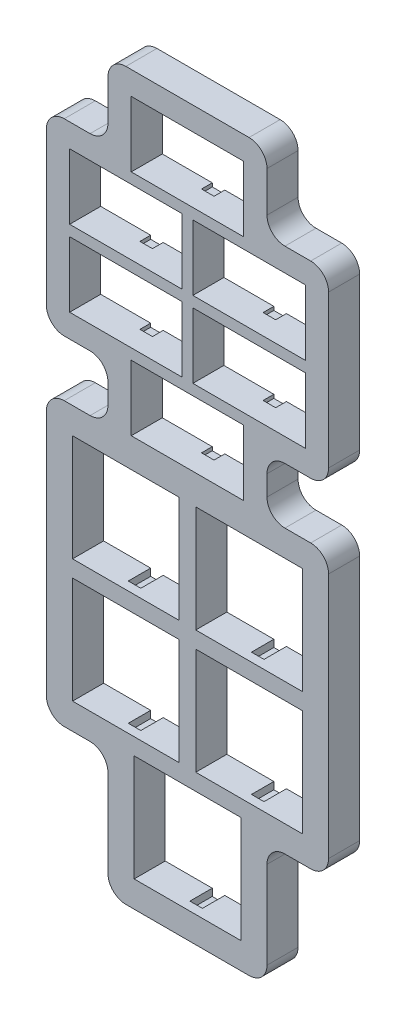
SolidWorks part; units mm, degrees
ref_plane "Front Plane" through (0, 0, 0) normal (0, 0, 1) x (1, 0, 0)
ref_plane "Top Plane" through (0, 0, 0) normal (0, 1, 0) x (1, 0, 0)
ref_plane "Right Plane" through (0, 0, 0) normal (1, 0, 0) x (0, 0, -1)
sketch "Sketch1" plane through (0, 0, 0) normal (0, 0, 1) x (1, 0, 0)
  line L0 (15.1765, -101.5047) -> (15.1765, -87.4077) construction
  line L1 (29.2735, -101.5047) -> (15.1765, -101.5047) construction
  line L2 (29.2735, -101.5047) -> (29.2735, -87.4077) construction
  line L3 (29.2735, -87.4077) -> (15.1765, -87.4077) construction
  line L4 (15.1765, -101.5047) -> (15.1765, -87.4077) construction
  line L5 (29.7815, -102.0127) -> (14.6685, -102.0127)
  line L6 (14.6685, -102.0127) -> (14.6685, -86.8997)
  line L7 (29.7815, -86.8997) -> (14.6685, -86.8997)
  line L8 (20.5423, -84.0423) -> (6.4453, -84.0423) construction
  line L9 (20.5423, -84.0423) -> (20.5423, -69.9453) construction
  line L10 (20.5423, -69.9453) -> (6.4453, -69.9453) construction
  line L11 (6.4453, -84.0423) -> (6.4453, -69.9453) construction
  line L12 (29.7815, -102.0127) -> (29.7815, -86.8997)
  line L13 (21.0503, -84.5503) -> (5.9373, -84.5503)
  line L14 (23.9078, -84.0422) -> (38.0048, -84.0422) construction
  line L15 (23.9078, -84.0422) -> (23.9078, -69.9452) construction
  line L16 (23.9078, -69.9452) -> (38.0048, -69.9452) construction
  line L17 (38.0048, -84.0422) -> (38.0048, -69.9452) construction
  line L18 (5.9373, -84.5503) -> (5.9373, -69.4373)
  line L19 (21.0503, -69.4373) -> (5.9373, -69.4373)
  line L20 (38.0048, -66.5797) -> (23.9078, -66.5797) construction
  line L21 (38.0048, -66.5797) -> (38.0048, -52.4827) construction
  line L22 (38.0048, -52.4827) -> (23.9078, -52.4827) construction
  line L23 (23.9078, -66.5797) -> (23.9078, -52.4827) construction
  line L24 (21.0503, -84.5503) -> (21.0503, -69.4373)
  line L25 (23.3998, -84.5502) -> (38.5128, -84.5502)
  line L26 (20.5423, -66.5798) -> (6.4453, -66.5797) construction
  line L27 (20.5423, -66.5798) -> (20.5423, -52.4827) construction
  line L28 (20.5423, -52.4827) -> (6.4453, -52.4828) construction
  line L29 (6.4453, -66.5797) -> (6.4453, -52.4828) construction
  line L30 (38.5128, -84.5502) -> (38.5128, -69.4372)
  line L31 (23.3998, -69.4372) -> (38.5128, -69.4372)
  line L32 (29.6863, -47.3075) -> (14.7638, -47.3075) construction
  line L33 (29.6863, -47.3075) -> (29.6863, -39.0525) construction
  line L34 (29.6863, -39.0525) -> (14.7638, -39.0525) construction
  line L35 (14.7638, -47.3075) -> (14.7638, -39.0525) construction
  line L36 (23.3998, -84.5502) -> (23.3998, -69.4372)
  line L37 (38.5128, -67.0877) -> (23.3998, -67.0877)
  line L38 (20.955, -36.5125) -> (6.0325, -36.5125) construction
  line L39 (20.955, -36.5125) -> (20.955, -28.2575) construction
  line L40 (20.955, -28.2575) -> (6.0325, -28.2575) construction
  line L41 (6.0325, -36.5125) -> (6.0325, -28.2575) construction
  line L42 (23.3998, -67.0877) -> (23.3998, -51.9747)
  line L43 (38.5128, -51.9747) -> (23.3998, -51.9747)
  line L44 (20.955, -25.7175) -> (6.0325, -25.7175) construction
  line L45 (20.955, -25.7175) -> (20.955, -17.4625) construction
  line L46 (20.955, -17.4625) -> (6.0325, -17.4625) construction
  line L47 (6.0325, -25.7175) -> (6.0325, -17.4625) construction
  line L48 (38.5128, -67.0877) -> (38.5128, -51.9747)
  line L49 (21.0503, -67.0877) -> (5.9373, -67.0877)
  line L50 (29.6863, -14.9225) -> (14.7638, -14.9225) construction
  line L51 (29.6863, -14.9225) -> (29.6863, -6.6675) construction
  line L52 (29.6863, -6.6675) -> (14.7638, -6.6675) construction
  line L53 (14.7638, -14.9225) -> (14.7638, -6.6675) construction
  line L54 (5.9373, -67.0877) -> (5.9373, -51.9747)
  line L55 (21.0503, -51.9747) -> (5.9373, -51.9747)
  line L56 (38.4175, -25.7175) -> (23.495, -25.7175) construction
  line L57 (38.4175, -25.7175) -> (38.4175, -17.4625) construction
  line L58 (38.4175, -17.4625) -> (23.495, -17.4625) construction
  line L59 (23.495, -25.7175) -> (23.495, -17.4625) construction
  line L60 (21.0503, -67.0877) -> (21.0503, -51.9747)
  line L61 (30.1943, -47.8155) -> (14.2558, -47.8155)
  line L62 (38.4175, -36.5125) -> (23.495, -36.5125) construction
  line L63 (38.4175, -36.5125) -> (38.4175, -28.2575) construction
  line L64 (38.4175, -28.2575) -> (23.495, -28.2575) construction
  line L65 (23.495, -36.5125) -> (23.495, -28.2575) construction
  line L66 (14.2558, -47.8155) -> (14.2558, -38.5445)
  line L67 (30.1943, -38.5445) -> (14.2558, -38.5445)
  line L68 (30.1943, -47.8155) -> (30.1943, -38.5445)
  line L69 (21.463, -37.0205) -> (5.5245, -37.0205)
  line L70 (5.5245, -37.0205) -> (5.5245, -27.7495)
  line L71 (21.463, -27.7495) -> (5.5245, -27.7495)
  line L72 (21.463, -37.0205) -> (21.463, -27.7495)
  line L73 (21.463, -26.2255) -> (5.5245, -26.2255)
  line L74 (5.5245, -26.2255) -> (5.5245, -16.9545)
  line L75 (21.463, -16.9545) -> (5.5245, -16.9545)
  line L76 (21.463, -26.2255) -> (21.463, -16.9545)
  line L77 (30.1943, -15.4305) -> (14.2558, -15.4305)
  line L78 (14.2558, -15.4305) -> (14.2558, -6.1595)
  line L79 (30.1943, -6.1595) -> (14.2558, -6.1595)
  line L80 (30.1943, -15.4305) -> (30.1943, -6.1595)
  line L81 (38.9255, -26.2255) -> (22.987, -26.2255)
  line L82 (22.987, -26.2255) -> (22.987, -16.9545)
  line L83 (38.9255, -16.9545) -> (22.987, -16.9545)
  line L84 (38.9255, -26.2255) -> (38.9255, -16.9545)
  line L85 (38.9255, -37.0205) -> (22.987, -37.0205)
  line L86 (22.987, -37.0205) -> (22.987, -27.7495)
  line L87 (38.9255, -27.7495) -> (22.987, -27.7495)
  line L88 (38.9255, -37.0205) -> (38.9255, -27.7495)
  line L97 (30.9563, -85.725) -> (39.6875, -85.725)
  line L98 (39.6875, -85.725) -> (39.6875, -50.8)
  line L99 (39.6875, -50.8) -> (4.7625, -50.8)
  line L100 (4.7625, -50.8) -> (4.7625, -85.725)
  line L101 (30.9563, -37.7825) -> (39.6875, -37.7825)
  line L102 (39.6875, -37.7825) -> (39.6875, -16.1925)
  line L103 (39.6875, -16.1925) -> (30.9563, -16.1925)
  line L104 (30.9563, -16.1925) -> (30.9563, -5.3975)
  line L105 (30.9563, -5.3975) -> (13.4938, -5.3975)
  line L106 (13.4938, -5.3975) -> (13.4938, -16.1925)
  line L107 (13.4938, -16.1925) -> (4.7625, -16.1925)
  line L108 (4.7625, -16.1925) -> (4.7625, -37.7825)
  line L109 (4.7625, -37.7825) -> (13.4938, -37.7825)
  line L110 (13.4938, -37.7825) -> (13.4938, -48.5775)
  line L111 (13.4938, -48.5775) -> (30.9563, -48.5775)
  line L112 (30.9563, -48.5775) -> (30.9563, -37.7825)
  line L113 (30.9563, -37.7825) -> (39.6875, -37.7825)
  line L114 (39.6875, -37.7825) -> (39.6875, -16.1925)
  line L115 (39.6875, -16.1925) -> (30.9563, -16.1925)
  line L116 (30.9563, -16.1925) -> (30.9563, -5.3975)
  line L117 (30.9563, -5.3975) -> (13.4938, -5.3975)
  line L118 (13.4938, -5.3975) -> (13.4938, -16.1925)
  line L119 (13.4938, -16.1925) -> (4.7625, -16.1925)
  line L120 (4.7625, -16.1925) -> (4.7625, -37.7825)
  line L121 (4.7625, -37.7825) -> (13.4938, -37.7825)
  line L122 (13.4938, -37.7825) -> (13.4938, -48.5775)
  line L124 (30.9563, -48.5775) -> (30.9563, -37.7825)
  line L125 (4.7625, -85.725) -> (13.4938, -85.725)
  line L126 (13.4938, -85.725) -> (13.4938, -103.1875)
  line L127 (13.4938, -103.1875) -> (30.9563, -103.1875)
  line L128 (30.9563, -103.1875) -> (30.9563, -85.725)
  line L129 (30.9563, -85.725) -> (39.6875, -85.725)
  line L130 (39.6875, -85.725) -> (39.6875, -50.8)
  line L131 (39.6875, -50.8) -> (30.9563, -50.8)
  line L132 (4.7625, -50.8) -> (4.7625, -85.725)
  line L133 (4.7625, -85.725) -> (13.4938, -85.725)
  line L134 (13.4938, -85.725) -> (13.4938, -103.1875)
  line L135 (13.4938, -103.1875) -> (30.9563, -103.1875)
  line L136 (30.9563, -103.1875) -> (30.9563, -85.725)
  line L2229 (13.4938, -50.8) -> (4.7625, -50.8)
  line L2231 (30.9563, -48.5775) -> (30.9563, -50.8)
  line L2233 (13.4938, -48.5775) -> (13.4938, -50.8)
  dimension "D1" = 0.508
  dimension "D2" = 0
  dimension "D3" = 0
extrude "Boss-Extrude1" add sketch "Sketch1" against normal up to surface (4.4025 mm away)
sketch "Sketch4" plane through (0, 0, -4.4025) normal (0, 0, -1) x (-1, 0, 0)
  line L40 (-30.9563, -37.7825) -> (-30.9563, -50.8)
  line L41 (-30.9563, -50.8) -> (-39.6875, -50.8)
  line L42 (-39.6875, -50.8) -> (-39.6875, -85.725)
  line L43 (-39.6875, -85.725) -> (-30.9563, -85.725)
  line L44 (-30.9563, -85.725) -> (-30.9563, -103.1875)
  line L45 (-30.9563, -103.1875) -> (-13.4938, -103.1875)
  line L46 (-13.4938, -103.1875) -> (-13.4938, -85.725)
  line L47 (-13.4938, -85.725) -> (-4.7625, -85.725)
  line L48 (-4.7625, -85.725) -> (-4.7625, -50.8)
  line L49 (-4.7625, -50.8) -> (-13.4938, -50.8)
  line L50 (-13.4938, -50.8) -> (-13.4938, -37.7825)
  line L51 (-13.4938, -37.7825) -> (-4.7625, -37.7825)
  line L52 (-4.7625, -37.7825) -> (-4.7625, -16.1925)
  line L53 (-4.7625, -16.1925) -> (-13.4938, -16.1925)
  line L54 (-13.4938, -16.1925) -> (-13.4938, -5.3975)
  line L55 (-13.4938, -5.3975) -> (-30.9563, -5.3975)
  line L56 (-30.9563, -5.3975) -> (-30.9563, -16.1925)
  line L57 (-30.9563, -16.1925) -> (-39.6875, -16.1925)
  line L58 (-39.6875, -16.1925) -> (-39.6875, -37.7825)
  line L59 (-39.6875, -37.7825) -> (-30.9563, -37.7825)
  line L60 (-30.9563, -37.7825) -> (-30.9563, -50.8)
  line L61 (-30.9563, -50.8) -> (-39.6875, -50.8)
  line L62 (-39.6875, -50.8) -> (-39.6875, -85.725)
  line L63 (-39.6875, -85.725) -> (-30.9563, -85.725)
  line L64 (-30.9563, -85.725) -> (-30.9563, -103.1875)
  line L65 (-30.9563, -103.1875) -> (-13.4938, -103.1875)
  line L66 (-13.4938, -103.1875) -> (-13.4938, -85.725)
  line L67 (-13.4938, -85.725) -> (-4.7625, -85.725)
  line L68 (-4.7625, -85.725) -> (-4.7625, -50.8)
  line L69 (-4.7625, -50.8) -> (-13.4938, -50.8)
  line L70 (-13.4938, -50.8) -> (-13.4938, -37.7825)
  line L71 (-13.4938, -37.7825) -> (-4.7625, -37.7825)
  line L72 (-4.7625, -37.7825) -> (-4.7625, -16.1925)
  line L73 (-4.7625, -16.1925) -> (-13.4938, -16.1925)
  line L74 (-13.4938, -16.1925) -> (-13.4938, -5.3975)
  line L75 (-13.4938, -5.3975) -> (-30.9563, -5.3975)
  line L76 (-30.9563, -5.3975) -> (-30.9563, -16.1925)
  line L77 (-30.9563, -16.1925) -> (-39.6875, -16.1925)
  line L78 (-39.6875, -16.1925) -> (-39.6875, -37.7825)
  line L79 (-39.6875, -37.7825) -> (-30.9563, -37.7825)
  dimension "D1" = 0
extrude "Extrude-Thin1" add sketch "Sketch4" against normal through all thin
fillet "Fillet1" radius 2.54 20 edges at (42.2275, -48.26, -2.2012) (2.2225, -13.6525, -2.2012) (10.9538, -2.8575, -2.2012) (33.4963, -2.8575, -2.2012) (42.2275, -13.6525, -2.2012) (42.2275, -40.3225, -2.2012) (2.2225, -40.3225, -2.2012) (2.2225, -48.26, -2.2012) (42.2275, -88.265, -2.2012) (33.4963, -105.7275, -2.2012) (10.9538, -105.7275, -2.2012) (2.2225, -88.265, -2.2012) (10.9538, -88.265, -2.2012) (33.4963, -88.265, -2.2012) (33.4963, -40.3225, -2.2012) (33.4963, -48.26, -2.2012) (10.9538, -48.26, -2.2012) (10.9538, -40.3225, -2.2012) (10.9538, -13.6525, -2.2012) (33.4963, -13.6525, -2.2012)
sketch "Sketch5" plane through (0, 0, -4.4025) normal (0, 0, -1) x (-1, 0, 0)
  line L0 (-14.2558, -6.1595) -> (-30.1943, -6.1595) construction
  line L1 (-26.5906, -6.1595) -> (-25.3206, -6.1595) construction
  line L2 (-26.5906, -6.1595) -> (-26.5906, -5.9065) construction
  line L3 (-26.5906, -5.9065) -> (-25.3206, -5.9065) construction
  line L4 (-25.3206, -6.1595) -> (-25.3206, -5.9065) construction
  line L5 (-19.1294, -6.1595) -> (-17.8594, -6.1595) construction
  line L6 (-19.1294, -6.1595) -> (-19.1294, -5.9065) construction
  line L7 (-19.1294, -5.9065) -> (-17.8594, -5.9065) construction
  line L8 (-17.8594, -6.1595) -> (-17.8594, -5.9065) construction
  line L9 (-21.59, -15.6835) -> (-21.59, -15.4305) construction
  line L10 (-22.86, -15.6835) -> (-21.59, -15.6835) construction
  line L11 (-22.86, -15.6835) -> (-22.86, -15.4305) construction
  line L12 (-22.86, -15.4305) -> (-21.59, -15.4305) construction
  line L13 (-35.3219, -16.7015) -> (-34.0519, -16.7015) construction
  line L14 (-27.8606, -16.7015) -> (-26.5906, -16.7015) construction
  line L15 (-30.3213, -26.4785) -> (-30.3213, -26.2255) construction
  line L16 (-31.5913, -26.4785) -> (-30.3213, -26.4785) construction
  line L17 (-35.3219, -16.9545) -> (-34.0519, -16.9545) construction
  line L18 (-34.0519, -16.9545) -> (-34.0519, -16.7015) construction
  line L19 (-27.8606, -16.9545) -> (-26.5906, -16.9545) construction
  line L20 (-26.5906, -16.9545) -> (-26.5906, -16.7015) construction
  line L21 (-31.5913, -26.2255) -> (-30.3213, -26.2255) construction
  line L22 (-27.8606, -16.9545) -> (-27.8606, -16.7015) construction
  line L23 (-31.5913, -26.4785) -> (-31.5913, -26.2255) construction
  line L24 (-35.3219, -16.9545) -> (-35.3219, -16.7015) construction
  line L25 (-12.8588, -26.4785) -> (-12.8588, -26.2255) construction
  line L26 (-16.5894, -16.9545) -> (-16.5894, -16.7015) construction
  line L27 (-10.3981, -16.9545) -> (-10.3981, -16.7015) construction
  line L28 (-14.1288, -26.4785) -> (-12.8588, -26.4785) construction
  line L29 (-14.1288, -26.4785) -> (-14.1288, -26.2255) construction
  line L30 (-17.8594, -16.7015) -> (-16.5894, -16.7015) construction
  line L31 (-9.1281, -16.9545) -> (-9.1281, -16.7015) construction
  line L32 (-14.1288, -26.2255) -> (-12.8588, -26.2255) construction
  line L33 (-17.8594, -16.9545) -> (-16.5894, -16.9545) construction
  line L34 (-10.3981, -16.9545) -> (-9.1281, -16.9545) construction
  line L35 (-17.8594, -16.9545) -> (-17.8594, -16.7015) construction
  line L36 (-10.3981, -16.7015) -> (-9.1281, -16.7015) construction
  line L37 (-30.3213, -37.2735) -> (-30.3213, -37.0205) construction
  line L38 (-31.5913, -37.2735) -> (-31.5913, -37.0205) construction
  line L39 (-27.8606, -27.7495) -> (-26.5906, -27.7495) construction
  line L40 (-10.3981, -27.7495) -> (-10.3981, -27.4965) construction
  line L41 (-17.8594, -27.4965) -> (-16.5894, -27.4965) construction
  line L42 (-31.5913, -37.0205) -> (-30.3213, -37.0205) construction
  line L43 (-14.1287, -37.2735) -> (-12.8587, -37.2735) construction
  line L44 (-35.3219, -27.4965) -> (-34.0519, -27.4965) construction
  line L45 (-31.5913, -37.2735) -> (-30.3213, -37.2735) construction
  line L46 (-12.8587, -37.2735) -> (-12.8587, -37.0205) construction
  line L47 (-26.5906, -27.7495) -> (-26.5906, -27.4965) construction
  line L48 (-9.1281, -27.7495) -> (-9.1281, -27.4965) construction
  line L49 (-16.5894, -27.7495) -> (-16.5894, -27.4965) construction
  line L50 (-17.8594, -27.7495) -> (-16.5894, -27.7495) construction
  line L51 (-27.8606, -27.7495) -> (-27.8606, -27.4965) construction
  line L52 (-10.3981, -27.7495) -> (-9.1281, -27.7495) construction
  line L53 (-34.0519, -27.7495) -> (-34.0519, -27.4965) construction
  line L54 (-35.3219, -27.7495) -> (-35.3219, -27.4965) construction
  line L55 (-17.8594, -27.7495) -> (-17.8594, -27.4965) construction
  line L56 (-35.3219, -27.7495) -> (-34.0519, -27.7495) construction
  line L57 (-14.1287, -37.2735) -> (-14.1287, -37.0205) construction
  line L58 (-14.1287, -37.0205) -> (-12.8587, -37.0205) construction
  line L59 (-27.8606, -27.4965) -> (-26.5906, -27.4965) construction
  line L60 (-10.3981, -27.4965) -> (-9.1281, -27.4965) construction
  line L61 (-22.86, -47.8155) -> (-21.59, -47.8155) construction
  line L62 (-26.5906, -38.5445) -> (-26.5906, -38.2915) construction
  line L63 (-21.59, -48.0685) -> (-21.59, -47.8155) construction
  line L64 (-25.3206, -38.5445) -> (-25.3206, -38.2915) construction
  line L65 (-22.86, -48.0685) -> (-21.59, -48.0685) construction
  line L66 (-19.1294, -38.5445) -> (-17.8594, -38.5445) construction
  line L67 (-19.1294, -38.2915) -> (-17.8594, -38.2915) construction
  line L68 (-26.5906, -38.5445) -> (-25.3206, -38.5445) construction
  line L69 (-22.86, -48.0685) -> (-22.86, -47.8155) construction
  line L70 (-19.1294, -38.5445) -> (-19.1294, -38.2915) construction
  line L71 (-17.8594, -38.5445) -> (-17.8594, -38.2915) construction
  line L72 (-26.5906, -38.2915) -> (-25.3206, -38.2915) construction
  line L73 (-26.8446, -6.4135) -> (-25.0666, -6.4135)
  line L74 (-25.0666, -6.4135) -> (-25.0666, -5.6525)
  line L75 (-26.8446, -5.6525) -> (-25.0666, -5.6525)
  line L76 (-26.8446, -6.4135) -> (-26.8446, -5.6525)
  line L77 (-19.3834, -6.4135) -> (-17.6054, -6.4135)
  line L78 (-17.6054, -6.4135) -> (-17.6054, -5.6525)
  line L79 (-19.3834, -5.6525) -> (-17.6054, -5.6525)
  line L80 (-19.3834, -6.4135) -> (-19.3834, -5.6525)
  line L81 (-21.336, -15.9375) -> (-21.336, -15.1765)
  line L82 (-23.114, -15.1765) -> (-21.336, -15.1765)
  line L83 (-23.114, -15.9375) -> (-23.114, -15.1765)
  line L84 (-23.114, -15.9375) -> (-21.336, -15.9375)
  line L85 (-35.5759, -16.4475) -> (-33.7979, -16.4475)
  line L86 (-33.7979, -17.2085) -> (-33.7979, -16.4475)
  line L87 (-35.5759, -17.2085) -> (-33.7979, -17.2085)
  line L88 (-35.5759, -17.2085) -> (-35.5759, -16.4475)
  line L89 (-28.1146, -16.4475) -> (-26.3366, -16.4475)
  line L90 (-26.3366, -17.2085) -> (-26.3366, -16.4475)
  line L91 (-28.1146, -17.2085) -> (-26.3366, -17.2085)
  line L92 (-28.1146, -17.2085) -> (-28.1146, -16.4475)
  line L93 (-30.0673, -26.7325) -> (-30.0673, -25.9715)
  line L94 (-31.8453, -25.9715) -> (-30.0673, -25.9715)
  line L95 (-31.8453, -26.7325) -> (-31.8453, -25.9715)
  line L96 (-31.8453, -26.7325) -> (-30.0673, -26.7325)
  line L97 (-12.6048, -26.7325) -> (-12.6048, -25.9715)
  line L98 (-14.3828, -25.9715) -> (-12.6048, -25.9715)
  line L99 (-14.3828, -26.7325) -> (-14.3828, -25.9715)
  line L100 (-14.3828, -26.7325) -> (-12.6048, -26.7325)
  line L101 (-16.3354, -17.2085) -> (-16.3354, -16.4475)
  line L102 (-18.1134, -16.4475) -> (-16.3354, -16.4475)
  line L103 (-18.1134, -17.2085) -> (-18.1134, -16.4475)
  line L104 (-18.1134, -17.2085) -> (-16.3354, -17.2085)
  line L105 (-10.6521, -17.2085) -> (-10.6521, -16.4475)
  line L106 (-10.6521, -16.4475) -> (-8.8741, -16.4475)
  line L107 (-8.8741, -17.2085) -> (-8.8741, -16.4475)
  line L108 (-10.6521, -17.2085) -> (-8.8741, -17.2085)
  line L109 (-30.0673, -37.5275) -> (-30.0673, -36.7665)
  line L110 (-31.8453, -36.7665) -> (-30.0673, -36.7665)
  line L111 (-31.8453, -37.5275) -> (-31.8453, -36.7665)
  line L112 (-31.8453, -37.5275) -> (-30.0673, -37.5275)
  line L113 (-28.1146, -28.0035) -> (-26.3366, -28.0035)
  line L114 (-26.3366, -28.0035) -> (-26.3366, -27.2425)
  line L115 (-28.1146, -27.2425) -> (-26.3366, -27.2425)
  line L116 (-28.1146, -28.0035) -> (-28.1146, -27.2425)
  line L117 (-10.6521, -28.0035) -> (-10.6521, -27.2425)
  line L118 (-10.6521, -27.2425) -> (-8.8741, -27.2425)
  line L119 (-8.8741, -28.0035) -> (-8.8741, -27.2425)
  line L120 (-10.6521, -28.0035) -> (-8.8741, -28.0035)
  line L121 (-18.1134, -27.2425) -> (-16.3354, -27.2425)
  line L122 (-16.3354, -28.0035) -> (-16.3354, -27.2425)
  line L123 (-18.1134, -28.0035) -> (-16.3354, -28.0035)
  line L124 (-18.1134, -28.0035) -> (-18.1134, -27.2425)
  line L125 (-14.3827, -37.5275) -> (-12.6047, -37.5275)
  line L126 (-12.6047, -37.5275) -> (-12.6047, -36.7665)
  line L127 (-14.3827, -36.7665) -> (-12.6047, -36.7665)
  line L128 (-14.3827, -37.5275) -> (-14.3827, -36.7665)
  line L129 (-35.5759, -27.2425) -> (-33.7979, -27.2425)
  line L130 (-33.7979, -28.0035) -> (-33.7979, -27.2425)
  line L131 (-35.5759, -28.0035) -> (-33.7979, -28.0035)
  line L132 (-35.5759, -28.0035) -> (-35.5759, -27.2425)
  line L133 (-23.114, -47.5615) -> (-21.336, -47.5615)
  line L134 (-21.336, -48.3225) -> (-21.336, -47.5615)
  line L135 (-23.114, -48.3225) -> (-21.336, -48.3225)
  line L136 (-23.114, -48.3225) -> (-23.114, -47.5615)
  line L137 (-26.8446, -38.7985) -> (-26.8446, -38.0375)
  line L138 (-26.8446, -38.0375) -> (-25.0666, -38.0375)
  line L139 (-25.0666, -38.7985) -> (-25.0666, -38.0375)
  line L140 (-26.8446, -38.7985) -> (-25.0666, -38.7985)
  line L141 (-19.3834, -38.7985) -> (-17.6054, -38.7985)
  line L142 (-17.6054, -38.7985) -> (-17.6054, -38.0375)
  line L143 (-19.3834, -38.0375) -> (-17.6054, -38.0375)
  line L144 (-19.3834, -38.7985) -> (-19.3834, -38.0375)
  dimension "D1" = 0.254
extrude "Cut-Extrude1" cut sketch "Sketch5" against normal blind 1.524
sketch "Sketch6" plane through (0, 0, -4.4025) normal (0, 0, -1) x (-1, 0, 0)
  line L0 (-23.3998, -51.9747) -> (-38.5128, -51.9747) construction
  line L1 (-35.1155, -51.9747) -> (-33.8455, -51.9747) construction
  line L2 (-35.1155, -51.9747) -> (-35.1155, -51.2127) construction
  line L3 (-35.1155, -51.2127) -> (-33.8455, -51.2127) construction
  line L4 (-33.8455, -51.9747) -> (-33.8455, -51.2127) construction
  line L5 (-28.067, -51.9747) -> (-28.067, -51.2127) construction
  line L6 (-28.067, -51.2127) -> (-26.797, -51.2127) construction
  line L7 (-28.067, -51.9747) -> (-26.797, -51.9747) construction
  line L8 (-26.797, -51.9747) -> (-26.797, -51.2127) construction
  line L9 (-30.3213, -67.8497) -> (-30.3213, -67.0877) construction
  line L10 (-31.5913, -67.8497) -> (-31.5913, -67.0877) construction
  line L11 (-31.5913, -67.0877) -> (-30.3213, -67.0877) construction
  line L12 (-31.5913, -67.8497) -> (-30.3213, -67.8497) construction
  line L13 (-10.6045, -51.9748) -> (-10.6045, -51.2128) construction
  line L14 (-12.8588, -67.8498) -> (-12.8588, -67.0878) construction
  line L15 (-17.653, -51.9748) -> (-17.653, -51.2128) construction
  line L16 (-16.383, -51.9748) -> (-16.383, -51.2128) construction
  line L17 (-10.6045, -51.9748) -> (-9.3345, -51.9748) construction
  line L18 (-9.3345, -51.9748) -> (-9.3345, -51.2128) construction
  line L19 (-10.6045, -51.2128) -> (-9.3345, -51.2128) construction
  line L20 (-14.1288, -67.8498) -> (-12.8588, -67.8498) construction
  line L21 (-17.653, -51.9748) -> (-16.383, -51.9748) construction
  line L22 (-14.1288, -67.8498) -> (-14.1288, -67.0878) construction
  line L23 (-17.653, -51.2128) -> (-16.383, -51.2128) construction
  line L24 (-14.1288, -67.0878) -> (-12.8588, -67.0878) construction
  line L25 (-30.3213, -85.3122) -> (-30.3213, -84.5502) construction
  line L26 (-31.5913, -85.3122) -> (-30.3213, -85.3122) construction
  line L27 (-14.1288, -84.5503) -> (-12.8588, -84.5503) construction
  line L28 (-35.1155, -69.4372) -> (-33.8455, -69.4372) construction
  line L29 (-9.3345, -69.4373) -> (-9.3345, -68.6753) construction
  line L30 (-35.1155, -68.6752) -> (-33.8455, -68.6752) construction
  line L31 (-17.653, -69.4373) -> (-16.383, -69.4373) construction
  line L32 (-17.653, -68.6753) -> (-16.383, -68.6753) construction
  line L33 (-28.067, -68.6752) -> (-26.797, -68.6752) construction
  line L34 (-17.653, -69.4373) -> (-17.653, -68.6753) construction
  line L35 (-35.1155, -69.4372) -> (-35.1155, -68.6752) construction
  line L36 (-31.5913, -85.3122) -> (-31.5913, -84.5502) construction
  line L37 (-12.8588, -85.3123) -> (-12.8588, -84.5503) construction
  line L38 (-28.067, -69.4372) -> (-26.797, -69.4372) construction
  line L39 (-14.1288, -85.3123) -> (-12.8588, -85.3123) construction
  line L40 (-16.383, -69.4373) -> (-16.383, -68.6753) construction
  line L41 (-31.5913, -84.5502) -> (-30.3213, -84.5502) construction
  line L42 (-33.8455, -69.4372) -> (-33.8455, -68.6752) construction
  line L43 (-28.067, -69.4372) -> (-28.067, -68.6752) construction
  line L44 (-26.797, -69.4372) -> (-26.797, -68.6752) construction
  line L45 (-10.6045, -69.4373) -> (-9.3345, -69.4373) construction
  line L46 (-14.1288, -85.3123) -> (-14.1288, -84.5503) construction
  line L47 (-10.6045, -68.6753) -> (-9.3345, -68.6753) construction
  line L48 (-10.6045, -69.4373) -> (-10.6045, -68.6753) construction
  line L49 (-26.3843, -86.8997) -> (-25.1143, -86.8997) construction
  line L50 (-21.59, -102.7747) -> (-21.59, -102.0127) construction
  line L51 (-22.86, -102.7747) -> (-22.86, -102.0127) construction
  line L52 (-26.3843, -86.1377) -> (-25.1143, -86.1377) construction
  line L53 (-22.86, -102.7747) -> (-21.59, -102.7747) construction
  line L54 (-22.86, -102.0127) -> (-21.59, -102.0127) construction
  line L55 (-19.3358, -86.1377) -> (-18.0658, -86.1377) construction
  line L56 (-26.3843, -86.8997) -> (-26.3843, -86.1377) construction
  line L57 (-25.1143, -86.8997) -> (-25.1143, -86.1377) construction
  line L58 (-18.0658, -86.8997) -> (-18.0658, -86.1377) construction
  line L59 (-19.3358, -86.8997) -> (-19.3358, -86.1377) construction
  line L60 (-19.3358, -86.8997) -> (-18.0658, -86.8997) construction
  line L61 (-35.3695, -52.2287) -> (-33.5915, -52.2287)
  line L62 (-33.5915, -52.2287) -> (-33.5915, -50.9587)
  line L63 (-35.3695, -50.9587) -> (-33.5915, -50.9587)
  line L64 (-35.3695, -52.2287) -> (-35.3695, -50.9587)
  line L65 (-28.321, -52.2287) -> (-28.321, -50.9587)
  line L66 (-28.321, -50.9587) -> (-26.543, -50.9587)
  line L67 (-26.543, -52.2287) -> (-26.543, -50.9587)
  line L68 (-28.321, -52.2287) -> (-26.543, -52.2287)
  line L69 (-30.0673, -68.1037) -> (-30.0673, -66.8337)
  line L70 (-31.8453, -66.8337) -> (-30.0673, -66.8337)
  line L71 (-31.8453, -68.1037) -> (-31.8453, -66.8337)
  line L72 (-31.8453, -68.1037) -> (-30.0673, -68.1037)
  line L73 (-10.8585, -52.2288) -> (-10.8585, -50.9588)
  line L74 (-10.8585, -50.9588) -> (-9.0805, -50.9588)
  line L75 (-9.0805, -52.2288) -> (-9.0805, -50.9588)
  line L76 (-10.8585, -52.2288) -> (-9.0805, -52.2288)
  line L77 (-12.6048, -68.1038) -> (-12.6048, -66.8338)
  line L78 (-14.3828, -66.8338) -> (-12.6048, -66.8338)
  line L79 (-14.3828, -68.1038) -> (-14.3828, -66.8338)
  line L80 (-14.3828, -68.1038) -> (-12.6048, -68.1038)
  line L81 (-17.907, -52.2288) -> (-17.907, -50.9588)
  line L82 (-17.907, -50.9588) -> (-16.129, -50.9588)
  line L83 (-16.129, -52.2288) -> (-16.129, -50.9588)
  line L84 (-17.907, -52.2288) -> (-16.129, -52.2288)
  line L85 (-30.0673, -85.5662) -> (-30.0673, -84.2962)
  line L86 (-31.8453, -84.2962) -> (-30.0673, -84.2962)
  line L87 (-31.8453, -85.5662) -> (-31.8453, -84.2962)
  line L88 (-31.8453, -85.5662) -> (-30.0673, -85.5662)
  line L89 (-14.3828, -84.2963) -> (-12.6048, -84.2963)
  line L90 (-12.6048, -85.5663) -> (-12.6048, -84.2963)
  line L91 (-14.3828, -85.5663) -> (-12.6048, -85.5663)
  line L92 (-14.3828, -85.5663) -> (-14.3828, -84.2963)
  line L93 (-35.3695, -69.6912) -> (-33.5915, -69.6912)
  line L94 (-33.5915, -69.6912) -> (-33.5915, -68.4212)
  line L95 (-35.3695, -68.4212) -> (-33.5915, -68.4212)
  line L96 (-35.3695, -69.6912) -> (-35.3695, -68.4212)
  line L97 (-9.0805, -69.6913) -> (-9.0805, -68.4213)
  line L98 (-10.8585, -68.4213) -> (-9.0805, -68.4213)
  line L99 (-10.8585, -69.6913) -> (-10.8585, -68.4213)
  line L100 (-10.8585, -69.6913) -> (-9.0805, -69.6913)
  line L101 (-17.907, -69.6913) -> (-16.129, -69.6913)
  line L102 (-16.129, -69.6913) -> (-16.129, -68.4213)
  line L103 (-17.907, -68.4213) -> (-16.129, -68.4213)
  line L104 (-17.907, -69.6913) -> (-17.907, -68.4213)
  line L105 (-28.321, -68.4212) -> (-26.543, -68.4212)
  line L106 (-26.543, -69.6912) -> (-26.543, -68.4212)
  line L107 (-28.321, -69.6912) -> (-26.543, -69.6912)
  line L108 (-28.321, -69.6912) -> (-28.321, -68.4212)
  line L109 (-26.6383, -87.1537) -> (-24.8603, -87.1537)
  line L110 (-24.8603, -87.1537) -> (-24.8603, -85.8837)
  line L111 (-26.6383, -85.8837) -> (-24.8603, -85.8837)
  line L112 (-26.6383, -87.1537) -> (-26.6383, -85.8837)
  line L113 (-21.336, -103.0287) -> (-21.336, -101.7587)
  line L114 (-23.114, -101.7587) -> (-21.336, -101.7587)
  line L115 (-23.114, -103.0287) -> (-23.114, -101.7587)
  line L116 (-23.114, -103.0287) -> (-21.336, -103.0287)
  line L117 (-19.5898, -85.8837) -> (-17.8118, -85.8837)
  line L118 (-17.8118, -87.1537) -> (-17.8118, -85.8837)
  line L119 (-19.5898, -87.1537) -> (-17.8118, -87.1537)
  line L120 (-19.5898, -87.1537) -> (-19.5898, -85.8837)
  point P7 (-34.0995, -51.2127)
  point P11 (-27.051, -51.2127)
  point P16 (-30.5753, -67.0877)
  point P22 (-16.637, -51.2128)
  point P26 (-9.5885, -51.2128)
  point P31 (-13.1128, -67.0878)
  point P37 (-34.0995, -68.6752)
  point P41 (-27.051, -68.6752)
  point P46 (-30.5753, -84.5502)
  point P52 (-16.637, -68.6753)
  point P56 (-9.5885, -68.6753)
  point P61 (-13.1128, -84.5503)
  point P67 (-25.3683, -86.1377)
  point P71 (-18.3198, -86.1377)
  point P76 (-21.844, -102.0127)
  dimension "D1" = 0.254
extrude "Cut-Extrude2" cut sketch "Sketch6" against normal blind 3.175
